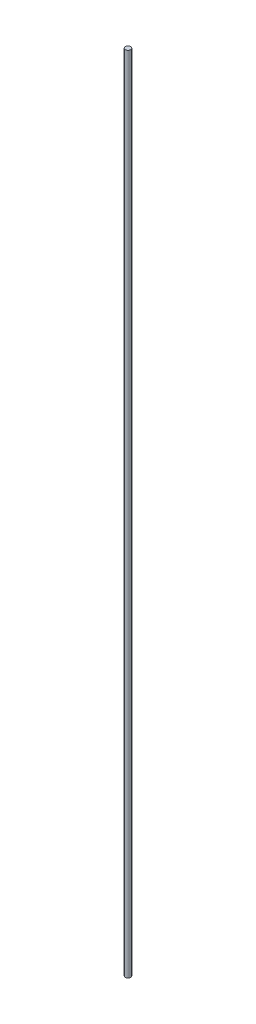
SolidWorks part; units mm, degrees
ref_plane "Front Plane" through (0, 0, 0) normal (0, 0, 1) x (1, 0, 0)
ref_plane "Top Plane" through (0, 0, 0) normal (0, 1, 0) x (1, 0, 0)
ref_plane "Right Plane" through (0, 0, 0) normal (1, 0, 0) x (0, 0, -1)
sketch "Sketch1" plane through (0, 0, 0) normal (0, 1, 0) x (1, 0, 0)
  circle A0 centre (0, 0) radius 1
  dimension "D1" = 2
extrude "Boss-Extrude1" add sketch "Sketch1" along normal blind 300
